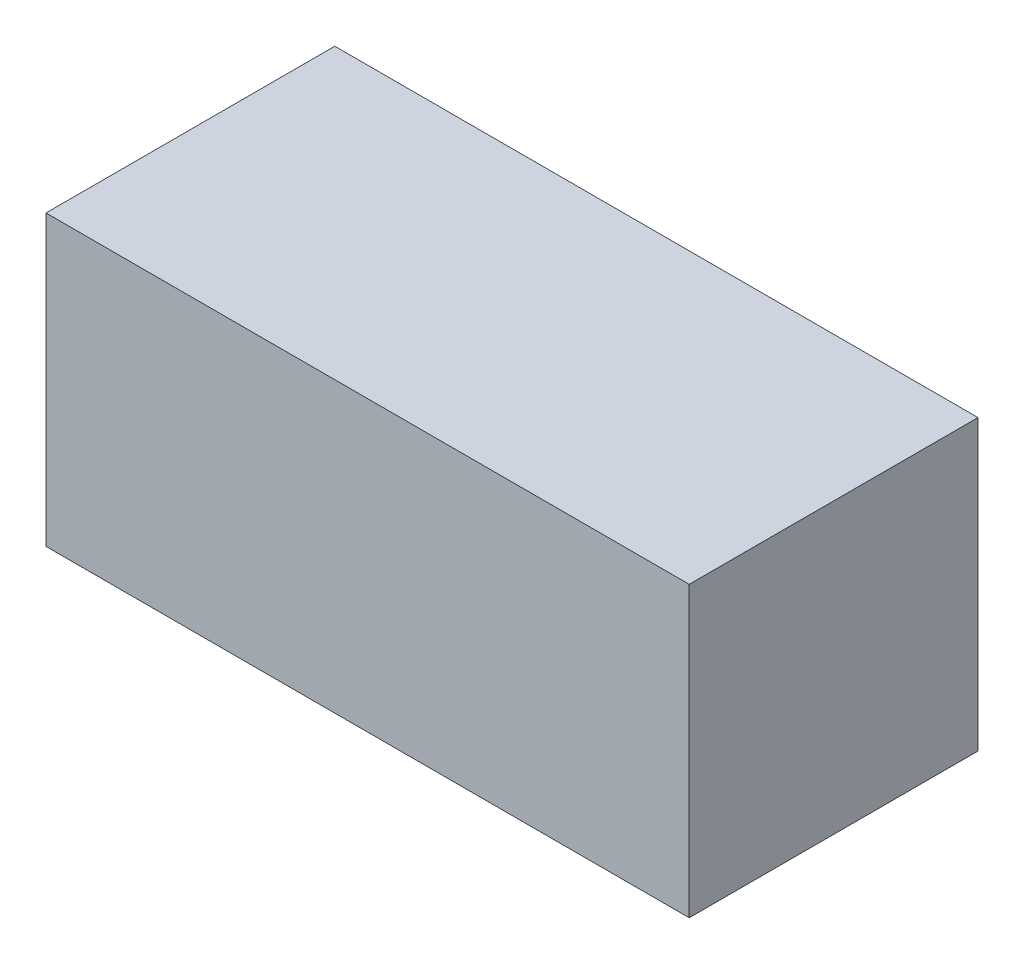
SolidWorks part; units mm, degrees
ref_plane "Front Plane" through (0, 0, 0) normal (0, 0, 1) x (1, 0, 0)
ref_plane "Top Plane" through (0, 0, 0) normal (0, 1, 0) x (1, 0, 0)
ref_plane "Right Plane" through (0, 0, 0) normal (1, 0, 0) x (0, 0, -1)
sketch "Sketch1" plane through (0, 0, 0) normal (0, 1, 0) x (1, 0, 0)
  line L1 (-2450, 1100) -> (2450, 1100)
  line L2 (-2450, 1100) -> (-2450, -1100)
  line L3 (-2450, -1100) -> (2450, -1100)
  line L4 (2450, 1100) -> (2450, -1100)
  line L5 (-2450, 1100) -> (2450, -1100) construction
  line L6 (-2450, -1100) -> (2450, 1100) construction
  point P0 (0, 0)
  dimension "D1" = 4900
  dimension "D2" = 2200
extrude "Boss-Extrude1" add sketch "Sketch1" along normal blind 2200
